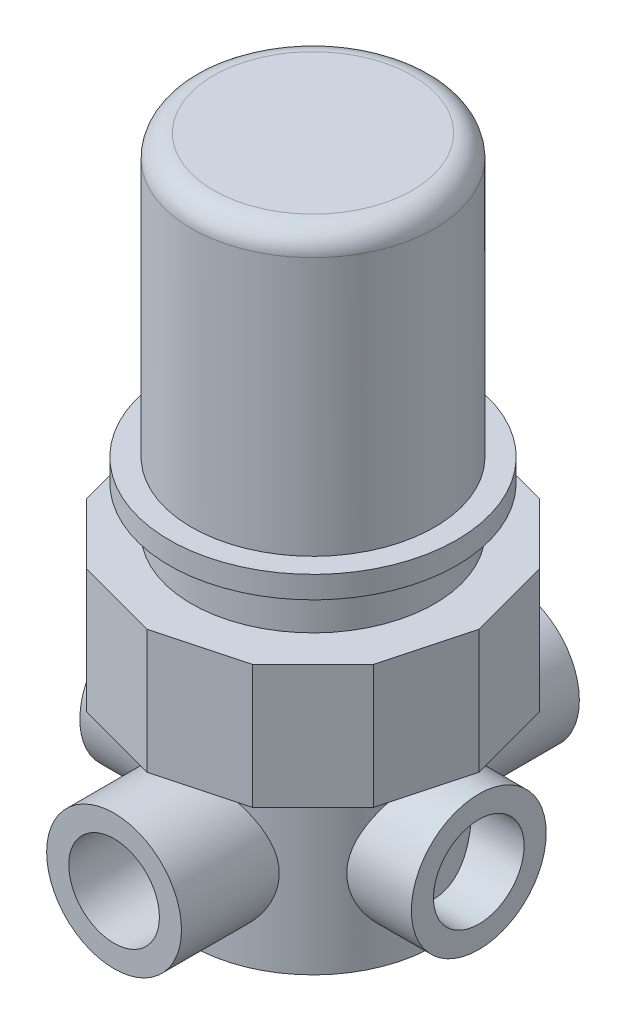
SolidWorks part; units mm, degrees
ref_plane "Front Plane" through (0, 0, 0) normal (0, 0, 1) x (1, 0, 0)
ref_plane "Top Plane" through (0, 0, 0) normal (0, 1, 0) x (1, 0, 0)
ref_plane "Right Plane" through (0, 0, 0) normal (1, 0, 0) x (0, 0, -1)
sketch "Sketch1" plane through (0, 0, 0) normal (0, 0, 1) x (1, 0, 0)
  line L0 (0, 73.914) -> (0, 0) construction
  line L1 (0, 73.914) -> (13.97, 73.914)
  line L2 (13.97, 73.914) -> (13.97, 41.656)
  line L3 (13.97, 41.656) -> (16.51, 41.656)
  line L4 (16.51, 41.656) -> (16.51, 39.116)
  line L5 (16.51, 39.116) -> (13.97, 39.116)
  line L6 (13.97, 39.116) -> (13.97, 34.036)
  line L7 (13.97, 34.036) -> (19.05, 34.036)
  line L8 (19.05, 34.036) -> (19.05, 19.812)
  line L9 (19.05, 19.812) -> (13.97, 19.812)
  line L10 (13.97, 19.812) -> (13.97, 0)
  line L11 (13.97, 0) -> (0, 0)
  line L12 (0, 73.914) -> (0, 0)
  dimension "D1" = 27.94
  dimension "D2" = 38.1
  dimension "D3" = 2.54
  dimension "D4" = 5.08
  dimension "D5" = 19.812
  dimension "D6" = 14.224
  dimension "D7" = 73.914
revolve "Revolve1" add sketch "Sketch1" angle 360 about L0
sketch "Sketch2" plane through (0, 34.036, 0) normal (0, 1, 0) x (1, 0, 0)
  line L1 (0, 19.05) -> (-9.525, 16.4978)
  line L2 (-9.525, 16.4978) -> (-16.4978, 9.525)
  line L3 (-16.4978, 9.525) -> (-19.05, 0)
  line L4 (-19.05, 0) -> (-16.4978, -9.525)
  line L5 (-16.4978, -9.525) -> (-9.525, -16.4978)
  line L6 (-9.525, -16.4978) -> (0, -19.05)
  line L7 (0, -19.05) -> (9.525, -16.4978)
  line L8 (9.525, -16.4978) -> (16.4978, -9.525)
  line L9 (16.4978, -9.525) -> (19.05, 0)
  line L10 (19.05, 0) -> (16.4978, 9.525)
  line L11 (16.4978, 9.525) -> (9.525, 16.4978)
  line L12 (9.525, 16.4978) -> (0, 19.05)
  circle A0 centre (0, 0) radius 18.4009 construction
  circle A1 centre (0, 0) radius 19.05 construction
  circle A3 centre (0, 0) radius 19.05
  circle M2 centre (0, 0) radius 19.05
extrude "Cut-Extrude1" cut sketch "Sketch2" against normal up to next contours L2 M2 | L3 M2 | L4 M2 | L5 M2 | L6 M2 | L7 M2 | L8 M2 | L9 M2 | L10 M2 | L11 M2 | L12 M2 | L1 M2 | A3
ref_plane "Plane1" through (0, 0, 13.97) normal (0, 0, 1) x (1, 0, 0)
sketch "Sketch3" plane through (0, 0, 13.97) normal (0, 0, 1) x (1, 0, 0)
  line L0 (0, 19.812) -> (0, 0) construction
  circle A0 centre (0, 9.906) radius 5.207
  circle A1 centre (0, 9.906) radius 7.747
  dimension "D1" = 10.414
  dimension "D2" = 2.54
extrude "Boss-Extrude1" add sketch "Sketch3" along normal blind 8.89 and the other way up to next
pattern_circular "CirPattern1" count 4 over 360 about axis through (0, 0, 0) along (0, 1, 0) of "Boss-Extrude1"
sketch "Sketch4" plane through (22.86, 0, 0) normal (1, 0, 0) x (0, 0, -1)
  circle A1 centre (0, 9.906) radius 7.747
  circle A2 centre (0, 9.906) radius 7.747
  dimension "D1" = 0
extrude "Cut-Extrude2" cut sketch "Sketch4" against normal blind 3.81
mirror "Mirror2" about plane through (0, 0, 0) normal (1, 0, 0) of "Cut-Extrude2"
fillet "Fillet1" radius 2.54 1 edges at (-13.97, 73.914, 0)
